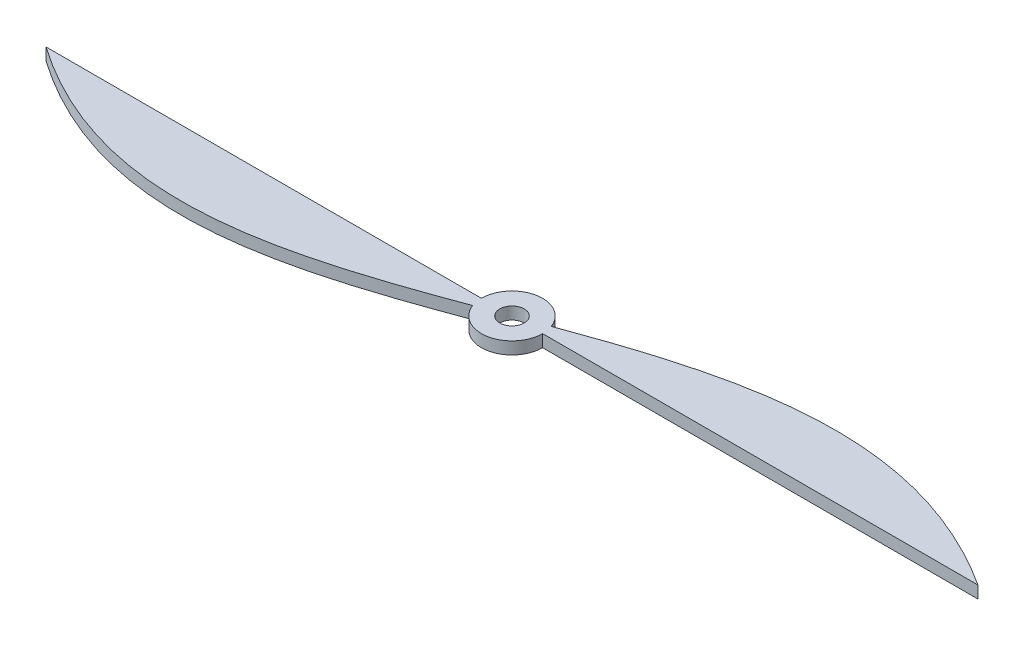
SolidWorks part; units mm, degrees
material "Thornel Mat VMA"
ref_plane "Plan de face" through (0, 0, 0) normal (0, 0, 1) x (1, 0, 0)
ref_plane "Plan de dessus" through (0, 0, 0) normal (0, 1, 0) x (1, 0, 0)
ref_plane "Plan de droite" through (0, 0, 0) normal (1, 0, 0) x (0, 0, -1)
sketch "Esquisse2" plane through (0, 0, 0) normal (0, 1, 0) x (1, 0, 0)
  line L0 (-76.2, 0) -> (76.2, 0)
  circle A0 centre (0, 0) radius 5
  circle A1 centre (0, 0) radius 2
  spline S0 degree 3 poles (-76.2, 0) (-23.193, -37.006) (20.432, 35.9782) (76.2, 0) knots 0 0 0 0 1 1 1 1
  dimension "D3" = 10
  dimension "D4" = 4
  dimension "D1" = 76.2
  dimension "D2" = 152.4
extrude "Boss.-Extru.1" add sketch "Esquisse2" along normal blind 2 contours L0 S0 A0 | S0 A0 L0 | S0 A0 L0 A1 | A1 S0 A0 L0 | S0 A1 L0 A0 | A0 S0 A1 L0
